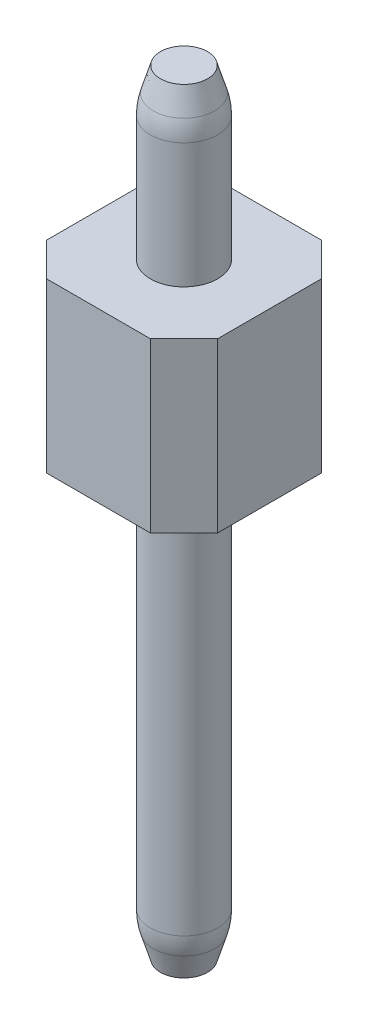
SolidWorks part; units mm, degrees
material "Brass"
ref_plane "Front Plane" through (0, 0, 0) normal (0, 0, 1) x (1, 0, 0)
ref_plane "Top Plane" through (0, 0, 0) normal (0, 1, 0) x (1, 0, 0)
ref_plane "Right Plane" through (0, 0, 0) normal (1, 0, 0) x (0, 0, -1)
sketch "Sketch1" plane through (0, 0, 0) normal (0, 1, 0) x (1, 0, 0)
  line L0 (0, 0) -> (2.54, 0) construction
  circle A0 centre (0, 0) radius 0.5
  circle A1 centre (2.54, 0) radius 0.5
  circle A2 centre (5.08, 0) radius 0.5
  circle A3 centre (7.62, 0) radius 0.5
  circle A4 centre (10.16, 0) radius 0.5
  circle A5 centre (12.7, 0) radius 0.5
  circle A6 centre (15.24, 0) radius 0.5
  circle A7 centre (17.78, 0) radius 0.5
  circle A8 centre (20.32, 0) radius 0.5
  circle A9 centre (22.86, 0) radius 0.5
  circle A10 centre (25.4, 0) radius 0.5
  circle A11 centre (27.94, 0) radius 0.5
  circle A12 centre (30.48, 0) radius 0.5
  circle A13 centre (33.02, 0) radius 0.5
  circle A14 centre (35.56, 0) radius 0.5
  circle A15 centre (38.1, 0) radius 0.5
  dimension "D1" = 1
  dimension "D3" = 2.54
  dimension "D2" = 16
extrude "Boss-Extrude1" add sketch "Sketch1" along normal blind 11.5
ref_plane "Plane1" through (0, 6.5, 0) normal (0, 1, 0) x (1, 0, 0)
sketch "Sketch2" plane through (0, 6.5, 0) normal (0, 1, 0) x (1, 0, 0)
  line L0 (-1.27, 0.77) -> (-0.77, 1.27)
  line L1 (-0.77, -1.27) -> (0.77, -1.27)
  line L2 (-1.27, -0.77) -> (-1.27, 0.77)
  line L3 (-0.77, 1.27) -> (0.77, 1.27)
  line L5 (-1.27, -1.27) -> (1.27, 1.27) construction
  line L6 (-1.27, 1.27) -> (1.27, -1.27) construction
  line L7 (0.77, 1.27) -> (1.27, 0.77)
  line L8 (0.77, -1.27) -> (1.27, -0.77)
  line L9 (-1.27, -0.77) -> (-0.77, -1.27)
  line L10 (1.27, 0.77) -> (1.77, 1.27)
  line L11 (1.77, 1.27) -> (3.31, 1.27)
  line L12 (3.31, 1.27) -> (3.81, 0.77)
  line L14 (3.31, -1.27) -> (3.81, -0.77)
  line L15 (1.77, -1.27) -> (3.31, -1.27)
  line L16 (1.27, -0.77) -> (1.77, -1.27)
  line L17 (3.81, 0.77) -> (4.31, 1.27)
  line L18 (4.31, 1.27) -> (5.85, 1.27)
  line L19 (5.85, 1.27) -> (6.35, 0.77)
  line L20 (6.35, -0.77) -> (6.35, 0.77) construction
  line L21 (5.85, -1.27) -> (6.35, -0.77)
  line L22 (4.31, -1.27) -> (5.85, -1.27)
  line L23 (3.81, -0.77) -> (4.31, -1.27)
  line L24 (6.35, 0.77) -> (6.85, 1.27)
  line L25 (6.85, 1.27) -> (8.39, 1.27)
  line L26 (8.39, 1.27) -> (8.89, 0.77)
  line L27 (8.89, -0.77) -> (8.89, 0.77) construction
  line L28 (8.39, -1.27) -> (8.89, -0.77)
  line L29 (6.85, -1.27) -> (8.39, -1.27)
  line L30 (6.35, -0.77) -> (6.85, -1.27)
  line L31 (8.89, 0.77) -> (9.39, 1.27)
  line L32 (9.39, 1.27) -> (10.93, 1.27)
  line L33 (10.93, 1.27) -> (11.43, 0.77)
  line L34 (11.43, -0.77) -> (11.43, 0.77) construction
  line L35 (10.93, -1.27) -> (11.43, -0.77)
  line L36 (9.39, -1.27) -> (10.93, -1.27)
  line L37 (8.89, -0.77) -> (9.39, -1.27)
  line L38 (11.43, 0.77) -> (11.93, 1.27)
  line L39 (11.93, 1.27) -> (13.47, 1.27)
  line L40 (13.47, 1.27) -> (13.97, 0.77)
  line L41 (13.97, -0.77) -> (13.97, 0.77) construction
  line L42 (13.47, -1.27) -> (13.97, -0.77)
  line L43 (11.93, -1.27) -> (13.47, -1.27)
  line L44 (11.43, -0.77) -> (11.93, -1.27)
  line L45 (13.97, 0.77) -> (14.47, 1.27)
  line L46 (14.47, 1.27) -> (16.01, 1.27)
  line L47 (16.01, 1.27) -> (16.51, 0.77)
  line L48 (16.51, -0.77) -> (16.51, 0.77) construction
  line L49 (16.01, -1.27) -> (16.51, -0.77)
  line L50 (14.47, -1.27) -> (16.01, -1.27)
  line L51 (13.97, -0.77) -> (14.47, -1.27)
  line L52 (16.51, 0.77) -> (17.01, 1.27)
  line L53 (17.01, 1.27) -> (18.55, 1.27)
  line L54 (18.55, 1.27) -> (19.05, 0.77)
  line L55 (19.05, -0.77) -> (19.05, 0.77) construction
  line L56 (18.55, -1.27) -> (19.05, -0.77)
  line L57 (17.01, -1.27) -> (18.55, -1.27)
  line L58 (16.51, -0.77) -> (17.01, -1.27)
  line L59 (19.05, 0.77) -> (19.55, 1.27)
  line L60 (19.55, 1.27) -> (21.09, 1.27)
  line L61 (21.09, 1.27) -> (21.59, 0.77)
  line L62 (21.59, -0.77) -> (21.59, 0.77) construction
  line L63 (21.09, -1.27) -> (21.59, -0.77)
  line L64 (19.55, -1.27) -> (21.09, -1.27)
  line L65 (19.05, -0.77) -> (19.55, -1.27)
  line L66 (21.59, 0.77) -> (22.09, 1.27)
  line L67 (22.09, 1.27) -> (23.63, 1.27)
  line L68 (23.63, 1.27) -> (24.13, 0.77)
  line L69 (24.13, -0.77) -> (24.13, 0.77) construction
  line L70 (23.63, -1.27) -> (24.13, -0.77)
  line L71 (22.09, -1.27) -> (23.63, -1.27)
  line L72 (21.59, -0.77) -> (22.09, -1.27)
  line L73 (24.13, 0.77) -> (24.63, 1.27)
  line L74 (24.63, 1.27) -> (26.17, 1.27)
  line L75 (26.17, 1.27) -> (26.67, 0.77)
  line L76 (26.67, -0.77) -> (26.67, 0.77) construction
  line L77 (26.17, -1.27) -> (26.67, -0.77)
  line L78 (24.63, -1.27) -> (26.17, -1.27)
  line L79 (24.13, -0.77) -> (24.63, -1.27)
  line L80 (26.67, 0.77) -> (27.17, 1.27)
  line L81 (27.17, 1.27) -> (28.71, 1.27)
  line L82 (28.71, 1.27) -> (29.21, 0.77)
  line L83 (29.21, -0.77) -> (29.21, 0.77) construction
  line L84 (28.71, -1.27) -> (29.21, -0.77)
  line L85 (27.17, -1.27) -> (28.71, -1.27)
  line L86 (26.67, -0.77) -> (27.17, -1.27)
  line L87 (29.21, 0.77) -> (29.71, 1.27)
  line L88 (29.71, 1.27) -> (31.25, 1.27)
  line L89 (31.25, 1.27) -> (31.75, 0.77)
  line L90 (31.75, -0.77) -> (31.75, 0.77) construction
  line L91 (31.25, -1.27) -> (31.75, -0.77)
  line L92 (29.71, -1.27) -> (31.25, -1.27)
  line L93 (29.21, -0.77) -> (29.71, -1.27)
  line L94 (31.75, 0.77) -> (32.25, 1.27)
  line L95 (32.25, 1.27) -> (33.79, 1.27)
  line L96 (33.79, 1.27) -> (34.29, 0.77)
  line L97 (34.29, -0.77) -> (34.29, 0.77) construction
  line L98 (33.79, -1.27) -> (34.29, -0.77)
  line L99 (32.25, -1.27) -> (33.79, -1.27)
  line L100 (31.75, -0.77) -> (32.25, -1.27)
  line L101 (34.29, 0.77) -> (34.79, 1.27)
  line L102 (34.79, 1.27) -> (36.33, 1.27)
  line L103 (36.33, 1.27) -> (36.83, 0.77)
  line L104 (36.83, -0.77) -> (36.83, 0.77) construction
  line L105 (36.33, -1.27) -> (36.83, -0.77)
  line L106 (34.79, -1.27) -> (36.33, -1.27)
  line L107 (34.29, -0.77) -> (34.79, -1.27)
  line L108 (36.83, 0.77) -> (37.33, 1.27)
  line L109 (37.33, 1.27) -> (38.87, 1.27)
  line L110 (38.87, 1.27) -> (39.37, 0.77)
  line L111 (39.37, -0.77) -> (39.37, 0.77)
  line L112 (38.87, -1.27) -> (39.37, -0.77)
  line L113 (37.33, -1.27) -> (38.87, -1.27)
  line L114 (36.83, -0.77) -> (37.33, -1.27)
  line L115 (-1.27, 0.77) -> (1.27, 0.77) construction
  point P0 (0, 0)
  dimension "D1" = 2.54
  dimension "D2" = 2.54
  dimension "D4" = 2.54
  dimension "D3" = 16
extrude "Boss-Extrude2" add sketch "Sketch2" along normal blind 2.5
chamfer "Chamfer1" distance 0.5 distance2 0.15 16 edges at (15.24, 11.5, 0.5) (12.7, 11.5, 0.5) (10.16, 11.5, 0.5) (7.62, 11.5, 0.5) (5.08, 11.5, 0.5) (2.54, 11.5, 0.5) (0, 11.5, 0.5) (38.1, 11.5, 0.5) (35.56, 11.5, 0.5) (33.02, 11.5, 0.5) (30.48, 11.5, 0.5) (27.94, 11.5, 0.5) (25.4, 11.5, 0.5) (22.86, 11.5, 0.5) (20.32, 11.5, 0.5) (17.78, 11.5, 0.5)
fillet "Fillet1" radius 1 16 edges at (38.1, 11, 0.5) (35.56, 11, 0.5) (33.02, 11, 0.5) (30.48, 11, 0.5) (27.94, 11, 0.5) (25.4, 11, 0.5) (22.86, 11, 0.5) (20.32, 11, 0.5) (17.78, 11, 0.5) (15.24, 11, 0.5) (12.7, 11, 0.5) (10.16, 11, 0.5) (7.62, 11, 0.5) (5.08, 11, 0.5) (2.54, 11, 0.5) (0, 11, 0.5)
chamfer "Chamfer2" distance 0.15 distance2 0.5 16 edges at (10.16, 0, 0.5) (17.78, 0, 0.5) (22.86, 0, 0.5) (27.94, 0, 0.5) (30.48, 0, 0.5) (0, 0, 0.5) (2.54, 0, 0.5) (5.08, 0, 0.5) (7.62, 0, 0.5) (12.7, 0, 0.5) (15.24, 0, 0.5) (20.32, 0, 0.5) (25.4, 0, 0.5) (33.02, 0, 0.5) (35.56, 0, 0.5) (38.1, 0, 0.5)
fillet "Fillet2" radius 1 16 edges at (30.48, 0.5, 0.5) (33.02, 0.5, 0.5) (35.56, 0.5, 0.5) (38.1, 0.5, 0.5) (27.94, 0.5, 0.5) (25.4, 0.5, 0.5) (22.86, 0.5, 0.5) (20.32, 0.5, 0.5) (17.78, 0.5, 0.5) (15.24, 0.5, 0.5) (12.7, 0.5, 0.5) (10.16, 0.5, 0.5) (7.62, 0.5, 0.5) (5.08, 0.5, 0.5) (2.54, 0.5, 0.5) (0, 0.5, 0.5)
sketch "Sketch3" plane through (0, 0, 1.27) normal (0, 0, 1) x (1, 0, 0)
  line L2 (1.27, 9) -> (1.27, 6.5) construction
  line L3 (1.27, 11.5) -> (1.27, 0)
  line L4 (1.27, 11.5) -> (39.37, 11.5)
  line L5 (39.37, 11.5) -> (39.37, 0)
  line L6 (39.37, 0) -> (1.27, 0)
extrude "Cut-Extrude1" cut sketch "Sketch3" against normal through all both and the other way through all
